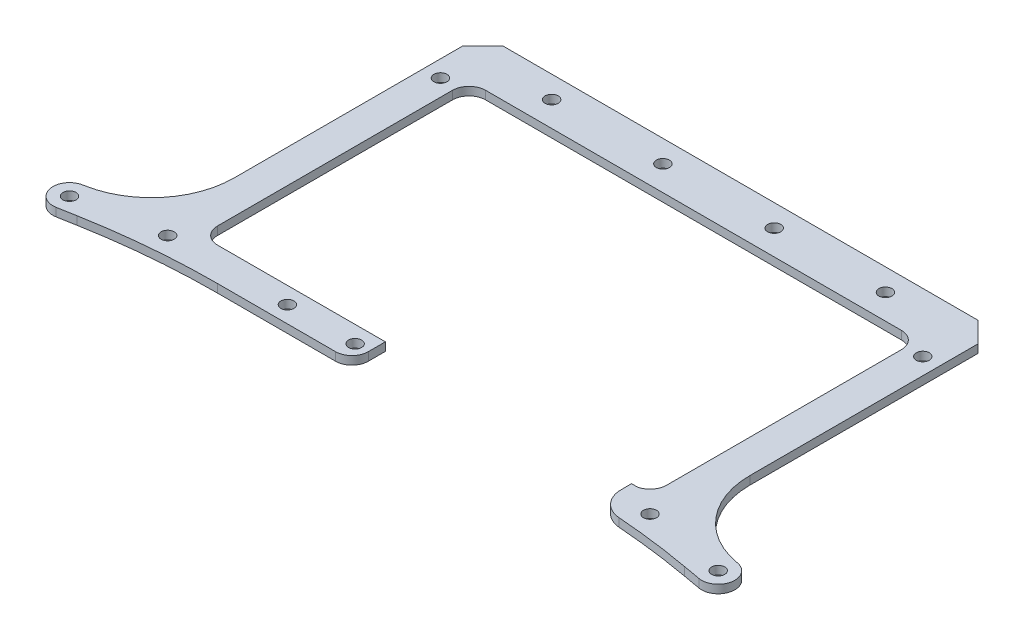
SolidWorks part; units mm, degrees
ref_plane "Front Plane" through (0, 0, 0) normal (0, 0, 1) x (1, 0, 0)
ref_plane "Top Plane" through (0, 0, 0) normal (0, 1, 0) x (1, 0, 0)
ref_plane "Right Plane" through (0, 0, 0) normal (1, 0, 0) x (0, 0, -1)
other "Bounding Box"
ref_plane "Default Plane" through (13.8565, 3.175, 6.7999) normal (0, -1, 0) x (-1, 0, 0)
sketch "Sketch1" plane through (0, 0, 0) normal (0, 1, 0) x (1, 0, 0)
  line L0 (-32.0376, 123.9797) -> (-115.8968, 123.9797) construction
  line L1 (-32.0376, 123.9797) -> (-111.4126, 123.9797)
  line L2 (53.6874, 27.9677) -> (53.6874, 126.8405) construction
  line L3 (-117.7626, 27.9677) -> (-117.7626, 126.8405) construction
  line L4 (53.6874, 27.9677) -> (53.6874, 117.6297)
  line L5 (-117.7626, 27.9677) -> (-117.7626, 117.6297)
  line L6 (-111.4126, 21.6177) -> (-47.4126, 21.6879)
  line L7 (46.4854, 21.7908) -> (48.8205, 21.7933)
  line L8 (-32.0376, 123.9797) -> (47.3374, 123.9797)
  line L14 (-47.4126, 15.1689) -> (-47.4126, 56.1328)
  line L15 (-41.1614, 62.3839) -> (43.1875, 62.3839)
  line L16 (46.0223, 59.5837) -> (46.4873, 21.6351)
  line L17 (46.4875, 21.6003) -> (46.4875, 17.7301)
  line L18 (83.9033, 4.5198) -> (90.6624, 3.3031)
  line L19 (92.9123, 15.8023) -> (92.4356, 15.8881)
  line L20 (66.3874, 47.0436) -> (66.3874, 134.1423)
  line L21 (66.3874, 134.1423) -> (58.5842, 141.9454)
  line L22 (58.5842, 141.9454) -> (-122.6595, 141.9454)
  line L23 (-122.6595, 141.9454) -> (-130.4626, 134.1423)
  line L24 (-130.4626, 134.1423) -> (-130.4626, 47.0436)
  line L25 (-156.5109, 15.8881) -> (-156.9876, 15.8023)
  line L26 (-154.7377, 3.3031) -> (-147.9786, 4.5198)
  line L27 (-98.7202, 8.9177) -> (-53.6638, 8.9177)
  line L28 (-47.4126, 15.1689) -> (-47.4126, 21.6879)
  line L30 (46.4854, 21.7908) -> (46.4873, 21.6351)
  line L31 (46.4875, 21.6003) -> (46.4875, 17.7301)
  line L32 (83.9033, 4.5198) -> (90.6624, 3.3031)
  line L33 (92.9123, 15.8023) -> (92.4356, 15.8881)
  line L34 (66.3874, 47.0436) -> (66.3874, 134.1423)
  line L35 (66.3874, 134.1423) -> (58.5842, 141.9454)
  line L36 (58.5842, 141.9454) -> (-122.6595, 141.9454)
  line L37 (-122.6595, 141.9454) -> (-130.4626, 134.1423)
  line L38 (-130.4626, 134.1423) -> (-130.4626, 47.0436)
  line L39 (-156.5109, 15.8881) -> (-156.9876, 15.8023)
  line L40 (-154.7377, 3.3031) -> (-147.9786, 4.5198)
  line L41 (-98.7202, 8.9177) -> (-53.6638, 8.9177)
  arc A1 (48.8205, 21.7933) -> (53.6874, 27.9677) centre (47.3374, 27.9677) ccw construction
  circle A2 centre (60.0374, 119.4077) radius 2.4892
  circle A3 centre (60.0374, 119.4077) radius 2.4892
  circle A4 centre (-52.5422, 15.2677) radius 2.4892
  circle A5 centre (-52.5422, 15.2677) radius 2.4892
  circle A6 centre (-78.3926, 15.2677) radius 2.4892
  circle A7 centre (-78.3926, 15.2677) radius 2.4892
  circle A8 centre (-10.7969, 133.5047) radius 2.4892
  circle A9 centre (-10.7969, 133.5047) radius 2.4892
  circle A10 centre (31.6846, 133.5047) radius 2.4892
  circle A11 centre (31.6846, 133.5047) radius 2.4892
  circle A12 centre (91.7874, 9.5527) radius 2.4892
  circle A13 centre (91.7874, 9.5527) radius 2.4892
  circle A24 centre (-53.2784, 133.5047) radius 2.4892
  circle A25 centre (-53.2784, 133.5047) radius 2.4892
  circle A26 centre (-95.7599, 133.5047) radius 2.4892
  circle A27 centre (-95.7599, 133.5047) radius 2.4892
  circle A28 centre (-124.1126, 15.2677) radius 2.4892
  circle A29 centre (-124.1126, 15.2677) radius 2.4892
  circle A30 centre (-155.8626, 9.5527) radius 2.4892
  circle A31 centre (-155.8626, 9.5527) radius 2.4892
  circle A32 centre (-124.1126, 119.4077) radius 2.4892
  circle A33 centre (-124.1126, 119.4077) radius 2.4892
  circle A34 centre (60.0374, 15.2677) radius 2.4892
  circle A35 centre (60.0374, 15.2677) radius 2.4892
  arc A36 (-117.7626, 27.9677) -> (-111.4126, 21.6177) centre (-111.4126, 27.9677) ccw construction
  arc A37 (48.8205, 21.7933) -> (53.6874, 27.9677) centre (47.3374, 27.9677) ccw
  arc A38 (-117.7626, 27.9677) -> (-111.4126, 21.6177) centre (-111.4126, 27.9677) ccw
  arc A39 (-111.4126, 123.9797) -> (-117.7626, 117.6297) centre (-111.4126, 117.6297) ccw
  arc A40 (53.6874, 117.6297) -> (47.3374, 123.9797) centre (47.3374, 117.6297) ccw
  arc A46 (-53.6638, 8.9177) -> (-47.4126, 15.1689) centre (-53.6638, 15.1689) ccw
  arc A47 (-41.1614, 62.3839) -> (-47.4126, 56.1328) centre (-41.1614, 56.1328) ccw
  arc A48 (46.0223, 59.5837) -> (43.1875, 62.3839) centre (43.1875, 59.5489) ccw
  arc A49 (46.4875, 21.6003) -> (46.4873, 21.6351) centre (43.6525, 21.6003) ccw
  arc A50 (46.4875, 17.7301) -> (55.3841, 8.1432) centre (56.1011, 17.7301) ccw
  arc A51 (83.9033, 4.5198) -> (55.3841, 8.1432) centre (34.6449, -269.1379) ccw
  arc A52 (90.6624, 3.3031) -> (92.9123, 15.8023) centre (91.7874, 9.5527) ccw
  arc A53 (66.3874, 47.0436) -> (92.4356, 15.8881) centre (98.0436, 47.0436) ccw
  arc A54 (-156.5109, 15.8881) -> (-130.4626, 47.0436) centre (-162.1189, 47.0436) ccw
  arc A55 (-156.9876, 15.8023) -> (-154.7377, 3.3031) centre (-155.8626, 9.5527) ccw
  arc A56 (-98.7202, 8.9177) -> (-147.9786, 4.5198) centre (-98.7202, -269.1379) ccw
  arc A57 (-53.6638, 8.9177) -> (-47.4126, 15.1689) centre (-53.6638, 15.1689) ccw
  arc A60 (46.4875, 21.6003) -> (46.4873, 21.6351) centre (43.6525, 21.6003) ccw
  arc A61 (46.4875, 17.7301) -> (55.3841, 8.1432) centre (56.1011, 17.7301) ccw
  arc A62 (83.9033, 4.5198) -> (55.3841, 8.1432) centre (34.6449, -269.1379) ccw
  arc A63 (90.6624, 3.3031) -> (92.9123, 15.8023) centre (91.7874, 9.5527) ccw
  arc A64 (66.3874, 47.0436) -> (92.4356, 15.8881) centre (98.0436, 47.0436) ccw
  arc A65 (-156.5109, 15.8881) -> (-130.4626, 47.0436) centre (-162.1189, 47.0436) ccw
  arc A66 (-156.9876, 15.8023) -> (-154.7377, 3.3031) centre (-155.8626, 9.5527) ccw
  arc A67 (-98.7202, 8.9177) -> (-147.9786, 4.5198) centre (-98.7202, -269.1379) ccw
  dimension "D1" = 0
  dimension "D2" = 0
  dimension "D3" = 0
  dimension "D4" = 0
  dimension "D5" = 0
  dimension "D6" = 0
  dimension "D12" = 0
  dimension "D13" = 0
  dimension "D14" = 0
  dimension "D15" = 0
  dimension "D16" = 0
  dimension "D17" = 0
  dimension "D18" = 0
extrude "Boss-Extrude1" add sketch "Sketch1" along normal blind 3.175
